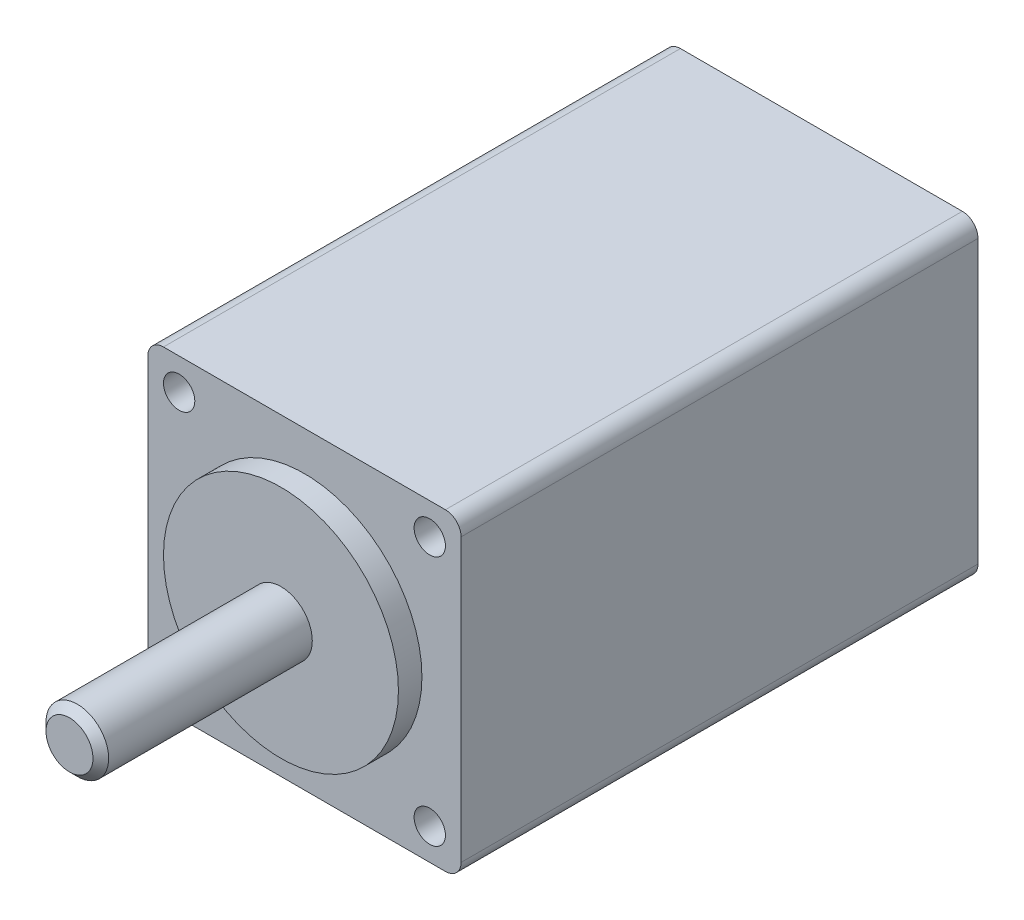
SolidWorks part; units mm, degrees
material "Plain Carbon Steel"
ref_plane "Front Plane" through (0, 0, 0) normal (0, 0, 1) x (1, 0, 0)
ref_plane "Top Plane" through (0, 0, 0) normal (0, 1, 0) x (1, 0, 0)
ref_plane "Right Plane" through (0, 0, 0) normal (1, 0, 0) x (0, 0, -1)
sketch "Sketch1" plane through (0, 0, 0) normal (0, 0, 1) x (1, 0, 0)
  line L0 (0, 0) -> (0, 10) construction
  line L1 (-10, 10) -> (10, 10)
  line L2 (-10, 10) -> (-10, -10)
  line L3 (-10, -10) -> (10, -10)
  line L4 (10, 10) -> (10, -10)
  line L5 (0, 0) -> (10, 0) construction
  dimension "D1" = 20
extrude "Boss-Extrude1" add sketch "Sketch1" against normal blind 33
sketch "Sketch2" plane through (0, 0, 0) normal (0, 0, 1) x (1, 0, 0)
  circle A0 centre (0, 0) radius 7.5
  dimension "D1" = 15
extrude "Boss-Extrude2" add sketch "Sketch2" along normal blind 1.5
sketch "Sketch3" plane through (0, 0, 1.5) normal (0, 0, 1) x (1, 0, 0)
  circle A0 centre (0, 0) radius 2
  dimension "D1" = 4
extrude "Cut-Extrude1" cut sketch "Sketch3" against normal through all
fillet "Fillet1" radius 1 4 edges at (-10, -10, -16.5) (10, -10, -16.5) (10, 10, -16.5) (-10, 10, -16.5)
sketch "Sketch4" plane through (0, 0, 0) normal (0, 0, 1) x (1, 0, 0)
  line L0 (8, 8) -> (8, -8) construction
  line L1 (8, -8) -> (-8, -8) construction
  line L2 (-8, -8) -> (-8, 8) construction
  line L3 (-8, 8) -> (8, 8) construction
  line L4 (0, 0) -> (0, 8) construction
  line L5 (0, 0) -> (8, 0) construction
  circle A0 centre (8, 8) radius 1
  circle A1 centre (-8, 8) radius 1
  circle A2 centre (-8, -8) radius 1
  circle A3 centre (8, -8) radius 1
  dimension "D1" = 2
  dimension "D2" = 16
extrude "Cut-Extrude2" cut sketch "Sketch4" against normal blind 3
sketch "Sketch5" plane through (0, 0, 0) normal (1, 0, 0) x (0, 0, -1)
  line L0 (-32.8575, 0) -> (0, 0) construction
  line L1 (-15, 2) -> (33, 2)
  line L2 (-15, 2) -> (-15, 0)
  line L3 (-15, 0) -> (33, 0)
  line L4 (33, 2) -> (33, 0)
  line L5 (33, -2) -> (33, 2) construction
  line L6 (0, -9) -> (0, 9) construction
  dimension "D1" = 4
  dimension "D2" = 15
revolve "Revolve1" add sketch "Sketch5" angle 360 about L0
chamfer "Chamfer1" distance 0.5 angle 45 2 edges at (2, 0, -33) (2, 0, 15)
